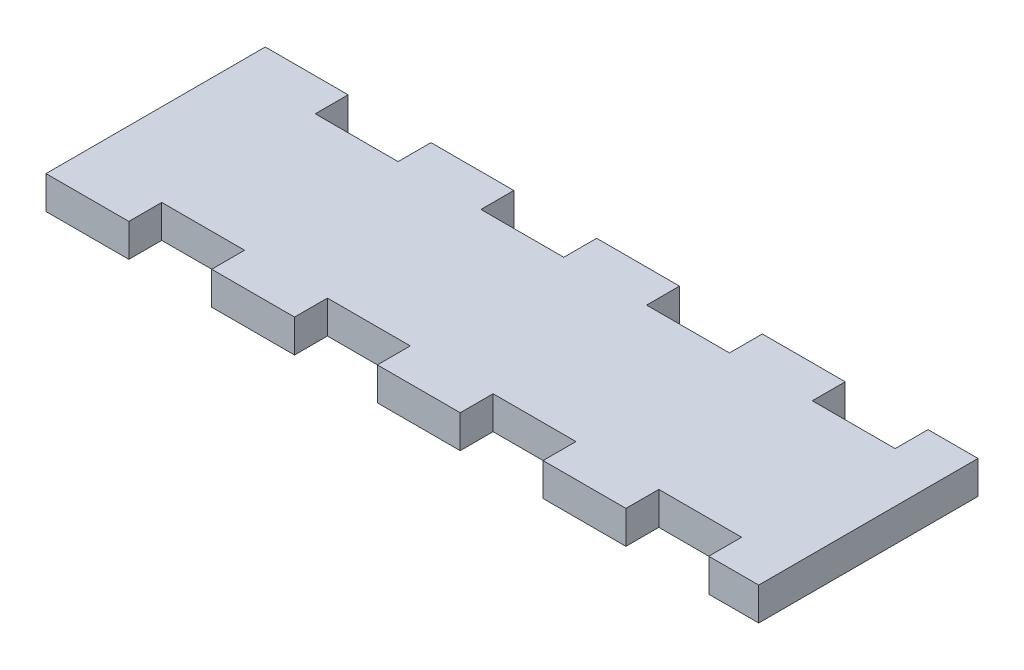
SolidWorks part; units mm, degrees
ref_plane "Front" through (0, 0, 0) normal (0, 0, 1) x (1, 0, 0)
ref_plane "Top" through (0, 0, 0) normal (0, 1, 0) x (1, 0, 0)
ref_plane "Right" through (0, 0, 0) normal (1, 0, 0) x (0, 0, -1)
sketch "Skizze1" plane through (0, 0, 0) normal (0, 1, 0) x (1, 0, 0)
  line L1 (0, 0) -> (65, 0) construction
  line L2 (0, 0) -> (0, 20) construction
  line L3 (0, 20) -> (65, 20) construction
  line L4 (65, 0) -> (65, 20) construction
  line L80 (0, 0) -> (7.556, 0)
  line L81 (7.556, 3) -> (7.556, 0)
  line L82 (7.556, 3) -> (15.1117, 3)
  line L83 (15.1117, 3) -> (15.1117, 0)
  line L84 (15.1117, 0) -> (22.6675, 0)
  line L85 (22.6675, 3) -> (22.6675, 0)
  line L86 (22.6675, 3) -> (30.2219, 3)
  line L87 (30.2219, 3) -> (30.2219, 0)
  line L88 (30.2219, 0) -> (37.7777, 0)
  line L89 (37.7777, 3) -> (37.7777, 0)
  line L90 (37.7777, 3) -> (45.3334, 3)
  line L91 (45.3334, 3) -> (45.3334, 0)
  line L92 (45.3334, 0) -> (52.8891, 0)
  line L93 (52.8891, 3) -> (52.8891, 0)
  line L94 (52.8891, 3) -> (60.4446, 3)
  line L95 (60.4446, 3) -> (60.4446, 0)
  line L96 (60.4446, 0) -> (65.0009, 0)
  line L97 (0, 20) -> (7.556, 20)
  line L98 (7.556, 20) -> (7.556, 17)
  line L99 (7.556, 17) -> (15.1117, 17)
  line L100 (15.1117, 20) -> (15.1117, 17)
  line L101 (15.1117, 20) -> (22.6675, 20)
  line L102 (22.6675, 20) -> (22.6675, 17)
  line L103 (22.6675, 17) -> (30.2219, 17)
  line L104 (30.2219, 20) -> (30.2219, 17)
  line L105 (30.2219, 20) -> (37.7777, 20)
  line L106 (37.7777, 20) -> (37.7777, 17)
  line L107 (37.7777, 17) -> (45.3334, 17)
  line L108 (45.3334, 20) -> (45.3334, 17)
  line L109 (45.3334, 20) -> (52.8891, 20)
  line L110 (52.8891, 20) -> (52.8891, 17)
  line L111 (52.8891, 17) -> (60.4446, 17)
  line L112 (60.4446, 20) -> (60.4446, 17)
  line L113 (60.4446, 20) -> (65.0009, 20)
  line L114 (0, 0) -> (0, 20)
  line L115 (65.0009, 0) -> (65.0009, 20)
  dimension "D1" = 20
  dimension "D2" = 65
  dimension "D3" = 3
extrude "Aufsatz-Linear austragen1" add sketch "Skizze1" along normal blind 3
